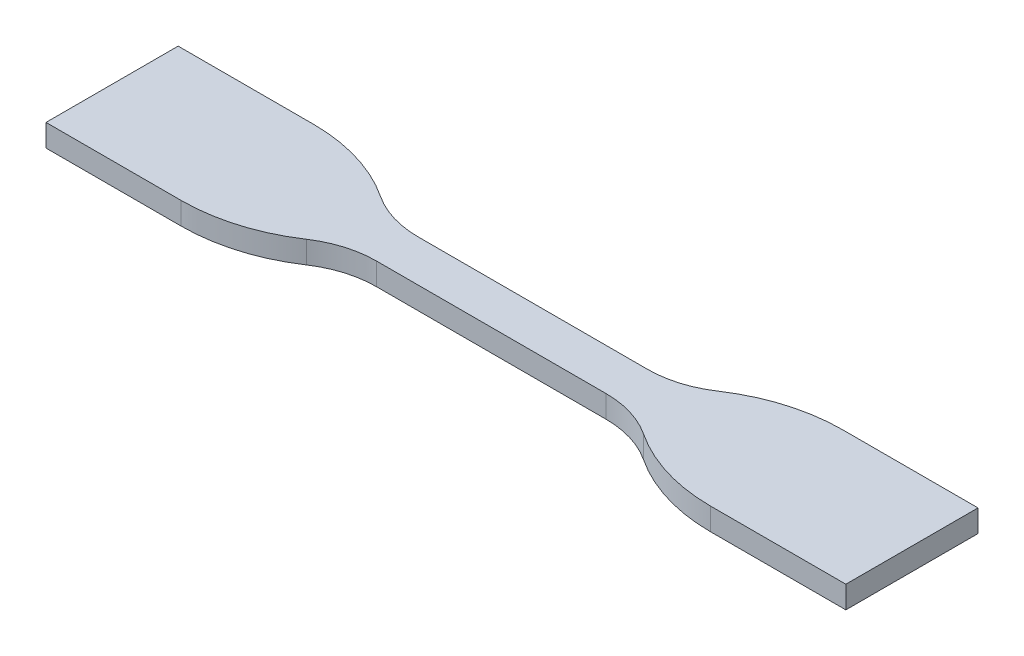
SolidWorks part; units mm, degrees
ref_plane "Alzado" through (0, 0, 0) normal (0, 0, 1) x (1, 0, 0)
ref_plane "Planta" through (0, 0, 0) normal (0, 1, 0) x (1, 0, 0)
ref_plane "Vista lateral" through (0, 0, 0) normal (1, 0, 0) x (0, 0, -1)
sketch "Croquis1" plane through (0, 0, 0) normal (0, 1, 0) x (1, 0, 0)
  line L0 (-16.5, 3) -> (16.5, 3)
  line L1 (-16.5, -3) -> (16.5, -3)
  line L2 (38.0581, 9.5) -> (57.5, 9.5)
  line L3 (57.5, 9.5) -> (57.5, -9.5)
  line L4 (57.5, -9.5) -> (38.0581, -9.5)
  line L5 (-38.0581, 9.5) -> (-57.5, 9.5)
  line L6 (-57.5, 9.5) -> (-57.5, -9.5)
  line L7 (-57.5, -9.5) -> (-38.0581, -9.5)
  line L8 (28.3216, -9.5) -> (-28.3216, -9.5) construction
  arc A0 (-16.5, 3) -> (-24.2388, 5.3333) centre (-16.5, 17) cw
  arc A3 (-16.5, -3) -> (-24.2388, -5.3333) centre (-16.5, -17) ccw
  arc A4 (16.5, 3) -> (24.2388, 5.3333) centre (16.5, 17) ccw
  arc A5 (16.5, -3) -> (24.2388, -5.3333) centre (16.5, -17) cw
  arc A6 (38.0581, -9.5) -> (24.2388, -5.3333) centre (38.0581, 15.5) cw
  arc A7 (38.0581, 9.5) -> (24.2388, 5.3333) centre (38.0581, -15.5) ccw
  arc A8 (-38.0581, -9.5) -> (-24.2388, -5.3333) centre (-38.0581, 15.5) ccw
  arc A9 (-38.0581, 9.5) -> (-24.2388, 5.3333) centre (-38.0581, -15.5) cw
  point P4 (0, -3)
  point P5 (0, 3)
  point P9 (57.5, 0)
  point P17 (0, -9.5)
  point P21 (-16.5, -1.3503)
  dimension "D2" = 14
  dimension "D6" = 25
  dimension "D1" = 6
  dimension "D3" = 19
  dimension "D4" = 33
  dimension "D5" = 115
extrude "Saliente-Extruir2" add sketch "Croquis1" along normal blind 3.2
